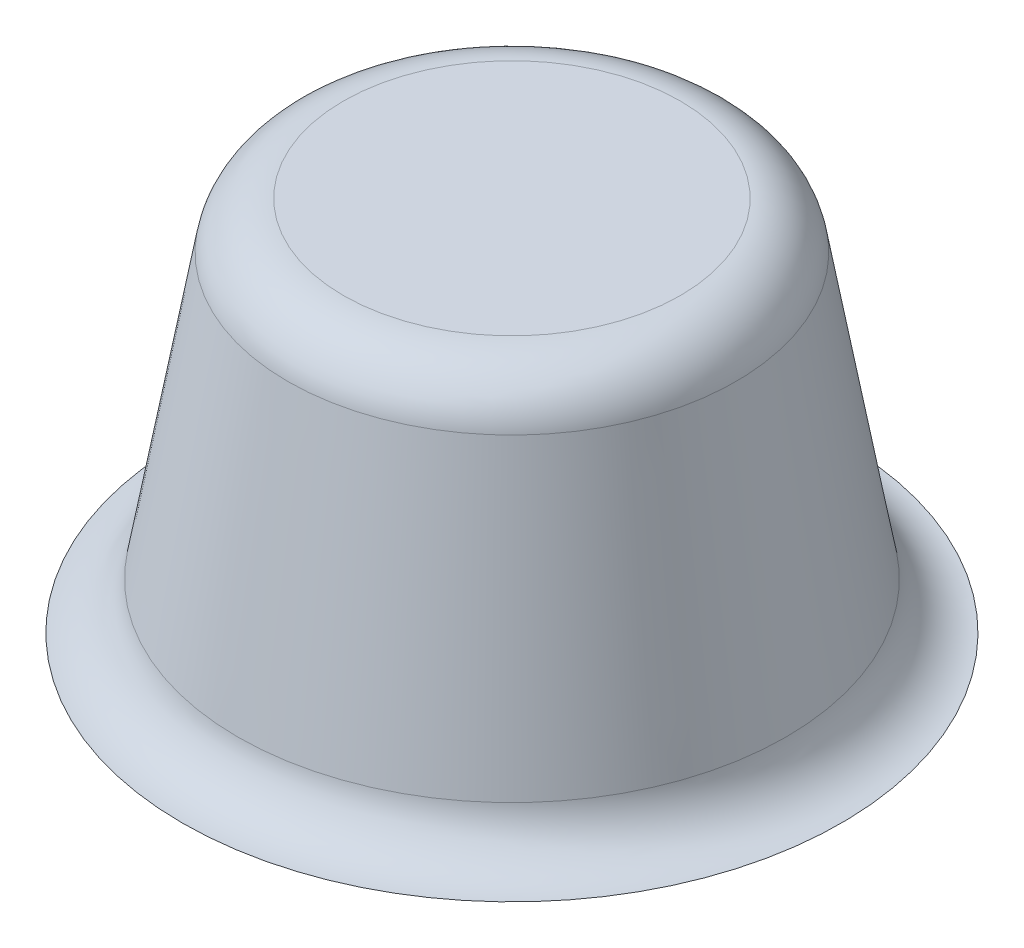
SolidWorks part; units mm, degrees
ref_plane "Front Plane" through (0, 0, 0) normal (0, 0, 1) x (1, 0, 0)
ref_plane "Top Plane" through (0, 0, 0) normal (0, 1, 0) x (1, 0, 0)
ref_plane "Right Plane" through (0, 0, 0) normal (1, 0, 0) x (0, 0, -1)
sketch "Sketch1" plane through (0, 0, 0) normal (0, 1, 0) x (1, 0, 0)
  line L1 (-15, 15) -> (15, 15)
  line L2 (-15, 15) -> (-15, -15)
  line L3 (-15, -15) -> (15, -15)
  line L4 (15, 15) -> (15, -15)
  line L5 (-15, 15) -> (15, -15) construction
  line L6 (-15, -15) -> (15, 15) construction
  point P0 (0, 0)
  dimension "D1" = 30
extrude "Boss-Extrude1" add sketch "Sketch1" against normal blind 1
sketch "Sketch2" plane through (0, 0, 0) normal (0, 1, 0) x (1, 0, 0)
  circle A0 centre (0, 0) radius 7.5
  dimension "D1" = 15
extrude "Boss-Extrude2" add sketch "Sketch2" along normal blind 10 draft 10
fillet "Fillet2" radius 1.5 2 edges at (0, 0, 7.5) (0, 10, 5.7367)
sketch3d "3DSketch4"
  line L0 (0, 1.2395, 0) -> (0, 8.7605, 0) construction
  line L1 (-5.456, 10, -1.7727) -> (0, 10, 0) construction
  line L2 (0, 10, 0) -> (3.372, 10, 4.6411) construction
  line L3 (0, 10, 0) -> (5.456, 10, -1.7727) construction
  line L4 (0, 10, 0) -> (0, 10, -5.7367) construction
  line L5 (0, 10, 0) -> (-3.372, 10, 4.6411) construction
  line L6 (-5.0634, 10, -2.6967) -> (-2.309, 10, -1.8017)
  line L7 (-1, 10, -2.7528) -> (-1, 10, -5.6489)
  line L8 (1, 10, -5.6489) -> (1, 10, -2.7528)
  line L9 (2.309, 10, -1.8017) -> (5.0634, 10, -2.6967)
  line L10 (-5.6814, 10, -0.7945) -> (-2.9271, 10, 0.1004)
  line L11 (-2.4271, 10, 1.6392) -> (-4.1294, 10, 3.9823)
  line L12 (-2.5113, 10, 5.1578) -> (-0.809, 10, 2.8148)
  line L13 (0.809, 10, 2.8148) -> (2.5113, 10, 5.1578)
  line L14 (2.4271, 10, 1.6392) -> (4.1294, 10, 3.9823)
  line L15 (2.9271, 10, 0.1004) -> (5.6814, 10, -0.7945)
  line L16 (0, 0, -15) -> (0, 0, -7.5) construction
  line L17 (15, 0, -15) -> (-15, 0, -15) construction
  line L18 (0, 10, 0) -> (0, 0, 0) construction
  line L19 (1, 10, -5.6489) -> (1, 0, -7.433)
  line L20 (-1, 10, -5.6489) -> (-1, 0, -7.433)
  line L21 (0, 0, 0) -> (-15, 0, -4.8738) construction
  line L22 (-15, 0, -15) -> (-15, 0, 15) construction
  line L23 (0, 0, 0) -> (-10.8981, 0, 15) construction
  line L24 (-15, 0, 15) -> (15, 0, 15) construction
  line L25 (0, 0, 0) -> (10.8981, 0, 15) construction
  line L26 (0, 0, 0) -> (15, 0, -4.8738) construction
  line L27 (15, 0, 15) -> (15, 0, -15) construction
  line L28 (-5.0634, 10, -2.6967) -> (-6.7602, 0, -3.248)
  line L29 (-5.6814, 10, -0.7945) -> (-7.3783, 0, -1.3459)
  line L30 (-4.1294, 10, 3.9823) -> (-5.178, 0, 5.4257)
  line L31 (-2.5113, 10, 5.1578) -> (-3.56, 0, 6.6012)
  line L32 (2.5113, 10, 5.1578) -> (3.56, 0, 6.6012)
  line L33 (4.1294, 10, 3.9823) -> (5.178, 0, 5.4257)
  line L34 (5.6814, 10, -0.7945) -> (7.3783, 0, -1.3459)
  line L35 (5.0634, 10, -2.6967) -> (6.7602, 0, -3.248)
  circle A0 centre (0, 10, 0) radius 5.7367
  arc A1 (1, 10, -2.7528) -> (2.309, 10, -1.8017) centre (2, 10, -2.7528) ccw
  arc A2 (2.4271, 10, 1.6392) -> (2.9271, 10, 0.1004) centre (3.2361, 10, 1.0515) ccw
  arc A3 (-0.809, 10, 2.8148) -> (0.809, 10, 2.8148) centre (0, 10, 3.4026) ccw
  arc A4 (-2.4271, 10, 1.6392) -> (-2.9271, 10, 0.1004) centre (-3.2361, 10, 1.0515) ccw
  arc A5 (-1, 10, -2.7528) -> (-2.309, 10, -1.8017) centre (-2, 10, -2.7528) ccw
  circle A6 centre (0, 10, 0) radius 5.7367 construction
  circle A7 centre (0, 0, 0) radius 7.5
  circle A8 centre (0, 0, 0) radius 7.5 construction
  circle A9 centre (0, 4, 0) radius 6.8115
  circle A10 centre (0, 6, 0) radius 6.4337
  point P2 (0, 15.7367, 0)
  point P27 (1, 10, -1.3764)
  point P28 (2, 11, -2.7528)
  point P31 (1.618, 10, 0.5257)
  point P32 (3.2361, 9, 1.0515)
  point P35 (0, 10, 1.7013)
  point P36 (0, 9, 3.4026)
  point P39 (-1.618, 10, 0.5257)
  point P40 (-3.2361, 11, 1.0515)
  point P43 (-1, 10, -1.3764)
  point P44 (-2, 9, -2.7528)
  point P47 (0, 4.2633, 0)
  point P51 (0, 7.5, 0)
  point P58 (0, 7.5, 0)
  point P81 (0.1674, 10.8094, 0.0282)
  point P84 (0.0831, 12.4327, -0.0833)
  dimension "D13" = 1
  dimension "D14" = 1
  dimension "D15" = 1
  dimension "D18" = 72
  dimension "D1" = 72
  dimension "D2" = 72
  dimension "D3" = 72
  dimension "D4" = 72
  dimension "D5" = 1
  dimension "D6" = 1
  dimension "D7" = 1
  dimension "D8" = 1
  dimension "D9" = 1
  dimension "D10" = 1
  dimension "D11" = 1
  dimension "D12" = 1
  dimension "D16" = 1
  dimension "D17" = 2
  dimension "D19" = 72
  dimension "D20" = 72
  dimension "D21" = 72
  dimension "D22" = 1
  dimension "D23" = 1
  dimension "D24" = 1
  dimension "D25" = 1
  dimension "D26" = 1
  dimension "D27" = 1
  dimension "D28" = 1
  dimension "D29" = 1
  dimension "D30" = 4
  dimension "D31" = 2
other "SurfaceCut2"
